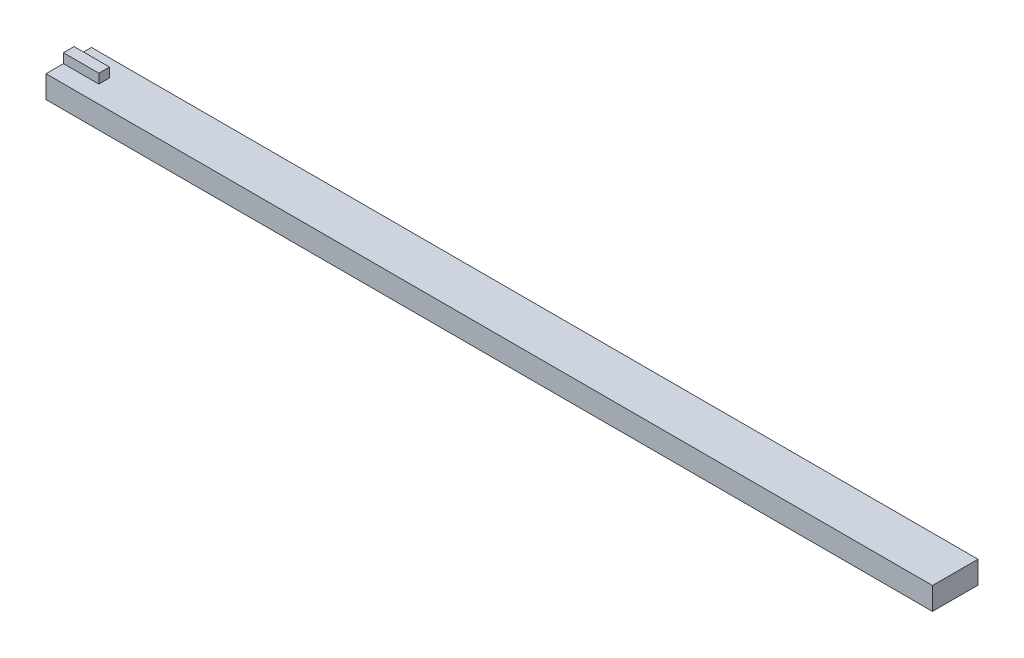
SolidWorks part; units mm, degrees
ref_plane "Front Plane" through (0, 0, 0) normal (0, 0, 1) x (1, 0, 0)
ref_plane "Top Plane" through (0, 0, 0) normal (0, 1, 0) x (1, 0, 0)
ref_plane "Right Plane" through (0, 0, 0) normal (1, 0, 0) x (0, 0, -1)
sketch "Sketch1" plane through (0, 0, 0) normal (1, 0, 0) x (0, 0, -1)
  line L1 (0, 0) -> (7.7, 0)
  line L2 (0, 0) -> (0, 3.8)
  line L3 (0, 3.8) -> (7.7, 3.8)
  line L4 (7.7, 0) -> (7.7, 3.8)
  dimension "D1" = 7.7
  dimension "D2" = 3.8
extrude "Boss-Extrude1" add sketch "Sketch1" along normal blind 150
sketch "Sketch2" plane through (0, 3.8, 0) normal (0, 1, 0) x (1, 0, 0)
  line L0 (0, 3.85) -> (150, 3.85) construction
  line L1 (0, 7.7) -> (0, 0) construction
  line L2 (150, 7.7) -> (150, 0) construction
  line L4 (6, 4.75) -> (0, 4.75)
  line L5 (6, 4.75) -> (6, 2.95)
  line L6 (6, 2.95) -> (0, 2.95)
  line L7 (0, 4.75) -> (0, 2.95)
  line L8 (6, 4.75) -> (0, 2.95) construction
  line L9 (6, 2.95) -> (0, 4.75) construction
  point P6 (3, 3.85)
  dimension "D1" = 6
  dimension "D2" = 1.8
extrude "Boss-Extrude2" add sketch "Sketch2" along normal blind 1.6
